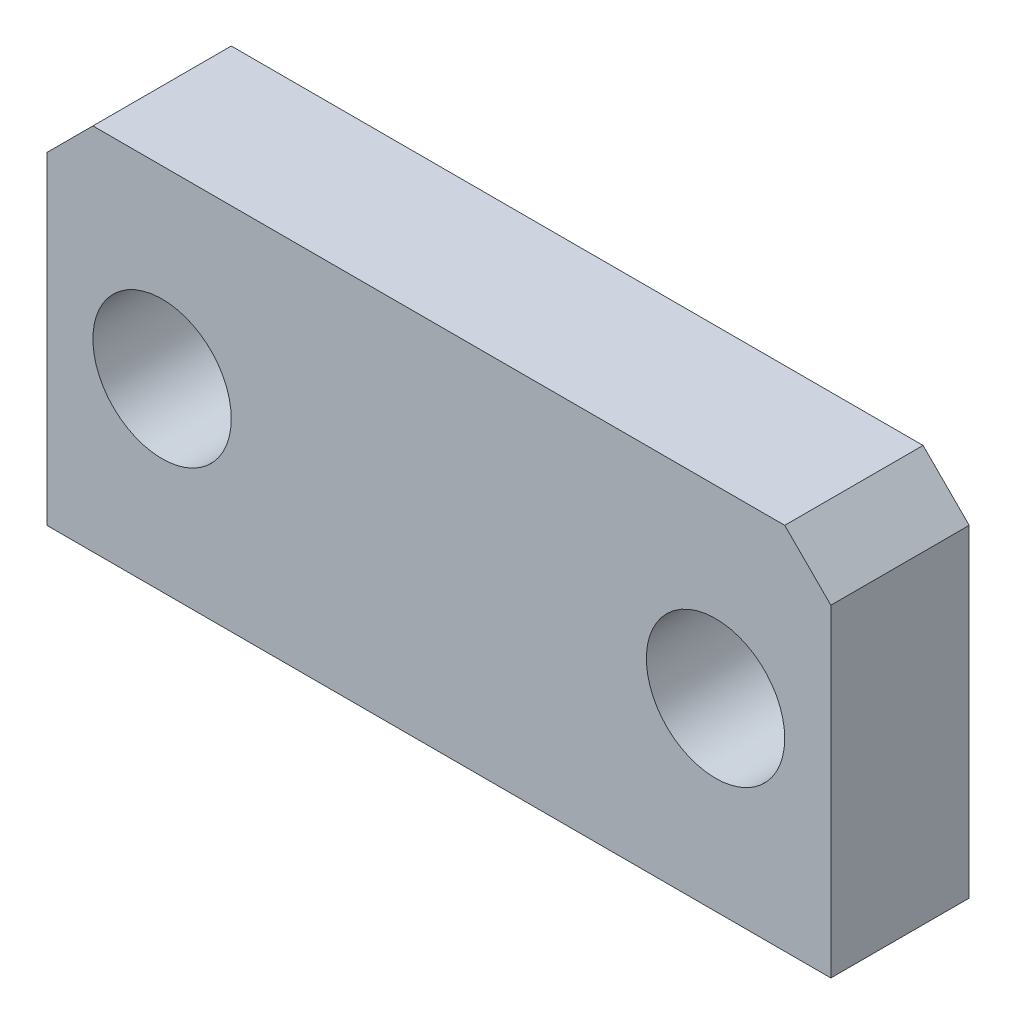
SolidWorks part; units mm, degrees
ref_plane "Plan de face" through (0, 0, 0) normal (0, 0, 1) x (1, 0, 0)
ref_plane "Plan de dessus" through (0, 0, 0) normal (0, 1, 0) x (1, 0, 0)
ref_plane "Plan de droite" through (0, 0, 0) normal (1, 0, 0) x (0, 0, -1)
sketch "Esquisse1" plane through (0, 0, 0) normal (0, 0, 1) x (1, 0, 0)
  line L0 (-8.5, 0) -> (8.5, 0) construction
  line L1 (-8.5, -4) -> (8.5, -4)
  line L2 (-8.5, -4) -> (-8.5, 4)
  line L3 (-8.5, 4) -> (8.5, 4)
  line L4 (8.5, -4) -> (8.5, 4)
  line L5 (-8.5, -4) -> (8.5, 4) construction
  line L6 (-8.5, 4) -> (8.5, -4) construction
  circle A0 centre (-6, 0) radius 1.5
  circle A1 centre (6, 0) radius 1.5
  point P0 (0, 0)
  dimension "D5" = 3
  dimension "D6" = 3
  dimension "D1" = 17
  dimension "D2" = 8
  dimension "D3" = 12
  dimension "D4" = 2.5
extrude "Boss.-Extru.1" add sketch "Esquisse1" along normal blind 3
chamfer "Chanfrein1" distance 1 angle 45 2 edges at (8.5, 4, 1.5) (-8.5, 4, 1.5)
